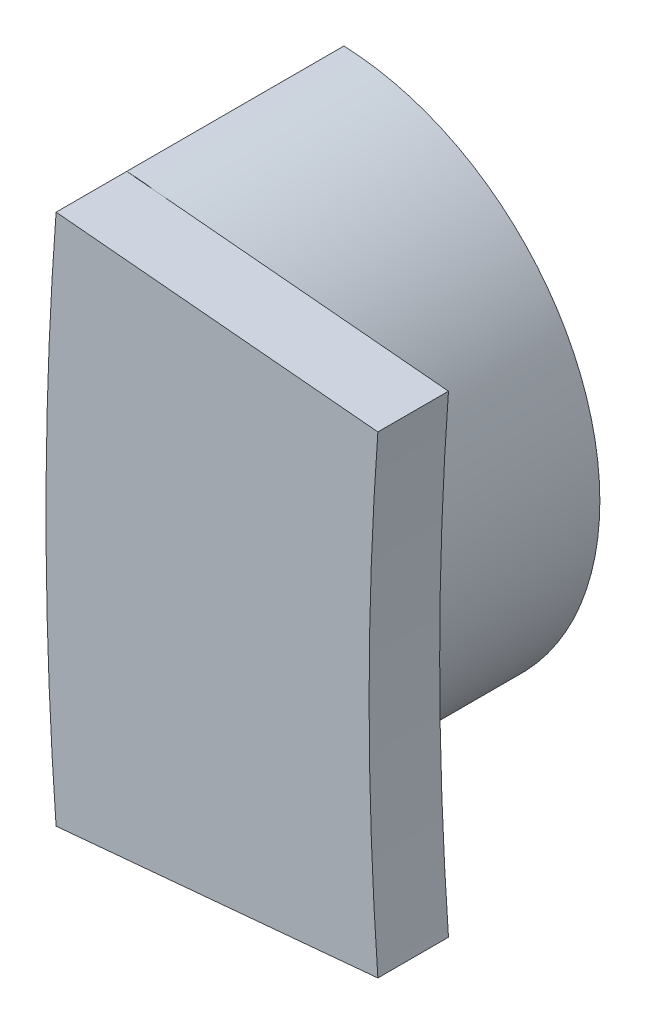
SolidWorks part; units mm, degrees
ref_plane "Front Plane" through (0, 0, 0) normal (0, 0, 1) x (1, 0, 0)
ref_plane "Top Plane" through (0, 0, 0) normal (0, 1, 0) x (1, 0, 0)
ref_plane "Right Plane" through (0, 0, 0) normal (1, 0, 0) x (0, 0, -1)
sketch "Sketch2" plane through (0, 0, 0) normal (0, 0, 1) x (1, 0, 0)
  line L0 (0, 0) -> (0, 57.4312) construction
  circle A0 centre (0, 0) radius 82.042 construction
  circle A1 centre (-82.042, 0) radius 6.35 construction
  arc A2 (-81.806, 6.2185) -> (-81.806, -6.2185) centre (-82.042, 0) cw
  arc A3 (-81.806, 6.2185) -> (-81.806, -6.2185) centre (0, 0) ccw
  dimension "D2" = 164.084
  dimension "D3" = 12.7
  dimension "D4" = 6.223
extrude "Boss-Extrude1" add sketch "Sketch2" along normal blind 5.08
sketch "Sketch3" plane through (0, 0, 5.08) normal (0, 0, 1) x (1, 0, 0)
  line L0 (0, 0) -> (-127.0411, 0) construction
  line L1 (-81.806, 6.2185) -> (-74.2799, 5.5304)
  line L2 (-81.806, -6.2185) -> (-74.2799, -5.5304)
  arc A0 (-81.806, 6.2185) -> (-81.806, -6.2185) centre (0, 0) ccw
  arc A1 (-74.2799, 5.5304) -> (-74.2799, -5.5304) centre (0, 0) ccw
  dimension "D1" = 74.4855
extrude "Boss-Extrude2" add sketch "Sketch3" along normal blind 1.651
ref_plane "Plane1" through (-82.042, 0, 0) normal (-1, 0, 0) x (0, 0, 1)
sketch "Sketch4" plane through (-82.042, 0, 0) normal (-1, 0, 0) x (0, 0, 1)
  line L0 (0, 6.2185) -> (0, -6.2185) construction
  circle A0 centre (3.683, 0) radius 1.0338
  dimension "D1" = 2.0676
  dimension "D2" = 3.683
extrude "Cut-Extrude1" cut sketch "Sketch4" against normal blind 3.175
